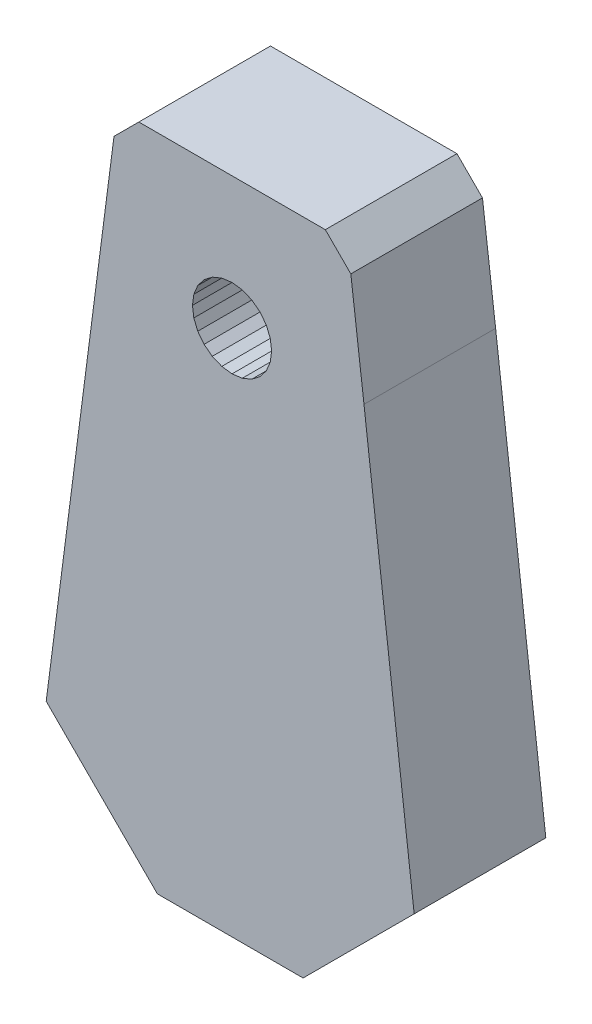
SolidWorks part; units mm, degrees
material "Maple"
ref_plane "Front Plane" through (0, 0, 0) normal (0, 0, 1) x (1, 0, 0)
ref_plane "Top Plane" through (0, 0, 0) normal (0, 1, 0) x (1, 0, 0)
ref_plane "Right Plane" through (0, 0, 0) normal (1, 0, 0) x (0, 0, -1)
sketch "Sketch1" plane through (0, 0, 0) normal (0, 0, 1) x (1, 0, 0)
  line L6268 (457.663, 187.9806) -> (464.305, 187.9806)
  line L6269 (452.5949, 193.0488) -> (457.663, 187.9806)
  line L6270 (455.6856, 216.8951) -> (456.8176, 218.0272)
  line L6271 (467.0798, 212.0137) -> (466.481, 216.8638)
  line L6272 (465.3176, 218.0272) -> (466.481, 216.8638)
  line L6273 (469.3678, 193.0435) -> (467.0798, 212.0137)
  line L6274 (465.3176, 218.0272) -> (456.8176, 218.0272)
  line L6275 (464.305, 187.9806) -> (469.3678, 193.0435)
  line L6276 (461.0664, 210.2097) -> (460.5994, 210.2711)
  line L6277 (460.5994, 210.2711) -> (460.1643, 210.4514)
  line L6278 (460.1643, 210.4514) -> (459.7907, 210.7381)
  line L6279 (459.7907, 210.7381) -> (459.504, 211.1117)
  line L6280 (459.504, 211.1117) -> (459.3238, 211.5468)
  line L6281 (459.3238, 211.5468) -> (459.2623, 212.0137)
  line L6282 (459.2623, 212.0137) -> (459.3238, 212.4806)
  line L6283 (459.3238, 212.4806) -> (459.504, 212.9157)
  line L6284 (459.504, 212.9157) -> (459.7907, 213.2894)
  line L6285 (459.7907, 213.2894) -> (460.1643, 213.5761)
  line L6286 (460.1643, 213.5761) -> (460.5994, 213.7563)
  line L6287 (460.5994, 213.7563) -> (461.0664, 213.8178)
  line L6288 (461.0664, 213.8178) -> (461.5333, 213.7563)
  line L6289 (461.5333, 213.7563) -> (461.9684, 213.5761)
  line L6290 (461.9684, 213.5761) -> (462.342, 213.2894)
  line L6291 (462.342, 213.2894) -> (462.6287, 212.9157)
  line L6292 (462.6287, 212.9157) -> (462.8089, 212.4806)
  line L6293 (462.8089, 212.4806) -> (462.8704, 212.0137)
  line L6294 (462.8704, 212.0137) -> (462.8089, 211.5468)
  line L6295 (462.8089, 211.5468) -> (462.6287, 211.1117)
  line L6296 (462.6287, 211.1117) -> (462.342, 210.7381)
  line L6297 (462.342, 210.7381) -> (461.9684, 210.4514)
  line L6298 (461.9684, 210.4514) -> (461.5333, 210.2711)
  line L6299 (461.5333, 210.2711) -> (461.0664, 210.2097)
  line L8419 (452.5949, 193.0488) -> (455.6856, 216.8951)
  line L9375 (459.6184, 197.7122) -> (459.6184, 197.4063)
  line L9376 (459.6184, 197.4063) -> (459.6385, 197.3101)
  line L9377 (459.6385, 197.3101) -> (459.6988, 197.2213)
  line L9378 (459.6988, 197.2213) -> (459.94, 197.066)
  line L9379 (459.94, 197.066) -> (460.3013, 196.9606)
  line L9380 (460.3013, 196.9606) -> (460.7423, 196.9255)
  line L9381 (460.7423, 196.9255) -> (461.1833, 196.9606)
  line L9382 (461.1833, 196.9606) -> (461.5447, 197.066)
  line L9383 (461.5447, 197.066) -> (461.7858, 197.2213)
  line L9384 (461.7858, 197.2213) -> (461.8461, 197.3101)
  line L9385 (461.8461, 197.3101) -> (461.8662, 197.4063)
  line L9386 (461.8662, 197.4063) -> (461.8662, 201.2151)
  line L9387 (461.8662, 201.2151) -> (461.8662, 197.4063)
  line L9388 (461.8662, 197.4063) -> (461.8461, 197.3101)
  line L9389 (461.8461, 197.3101) -> (461.7858, 197.2213)
  line L9390 (461.7858, 197.2213) -> (461.5447, 197.066)
  line L9391 (461.5447, 197.066) -> (461.1833, 196.9606)
  line L9392 (461.1833, 196.9606) -> (460.7423, 196.9255)
  line L9393 (460.7423, 196.9255) -> (460.3013, 196.9606)
  line L9394 (460.3013, 196.9606) -> (459.94, 197.066)
  line L9395 (459.94, 197.066) -> (459.6988, 197.2213)
  line L9396 (459.6988, 197.2213) -> (459.6385, 197.3101)
  line L9397 (459.6385, 197.3101) -> (459.6184, 197.4063)
  line L9398 (459.6184, 197.4063) -> (459.6184, 197.7122)
extrude "Boss-Extrude1" add sketch "Sketch1" along normal blind 6
